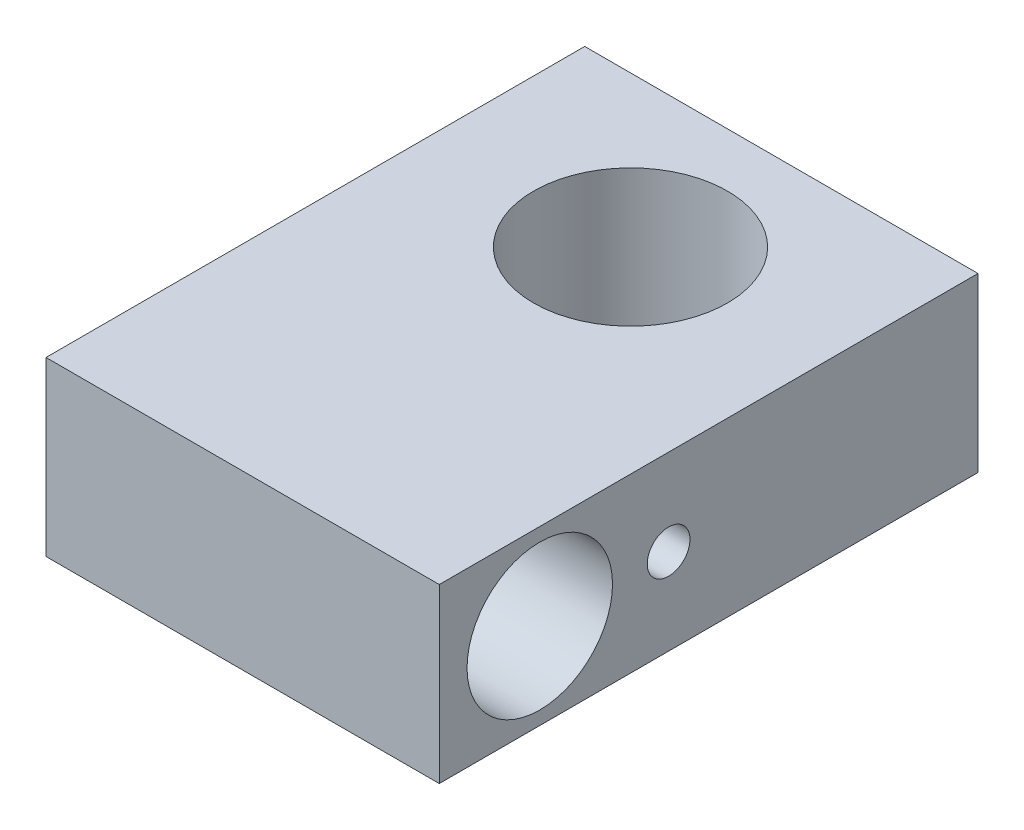
SolidWorks part; units mm, degrees
material "6061-T6 (SS)"
ref_plane "Front Plane" through (0, 0, 0) normal (0, 0, 1) x (1, 0, 0)
ref_plane "Top Plane" through (0, 0, 0) normal (0, 1, 0) x (1, 0, 0)
ref_plane "Right Plane" through (0, 0, 0) normal (1, 0, 0) x (0, 0, -1)
sketch "Sketch1" plane through (0, 0, 0) normal (0, 1, 0) x (1, 0, 0)
  line L0 (9.125, 7) -> (9.125, -18)
  line L1 (9.125, -18) -> (-9.125, -18)
  line L2 (-9.125, -18) -> (-9.125, 7)
  line L4 (-9.125, 7) -> (9.125, 7)
  line L8 (0, 0) -> (0, 7) construction
  point P4 (9.125, -18)
  point P6 (-9.125, -18)
  point P11 (-9.125, 7)
  point P12 (9.125, 7)
  dimension "D1" = 7
  dimension "D2" = 25
  dimension "D3" = 18.25
extrude "Boss-Extrude1" add sketch "Sketch1" along normal blind 8
hole_wizard "M10x1.0 Tapped Hole1" positions "Sketch3" profile "Sketch2" tap size "M10x1.0" standard "Ansi Metric" end condition through all
sketch "Sketch3" plane through (0, 8, 0) normal (0, 1, 0) x (-1, 0, 0)
  point P0 (0, 0)
sketch "Sketch2" plane through (0, 8, 0) normal (1, 0, 0) x (0, 0, 1)
  line L0 (0, 0) -> (0, 8)
  line L1 (0, 8) -> (4.5, 8)
  line L2 (4.5, 8) -> (4.5, 0)
  line L5 (4.5, 0) -> (0, 0)
  line L11 (0, -6.35) -> (0, 107.95) construction
  dimension "Thru Tap Drill Dia." = 9
  dimension "Thru Tap Drill Depth" = 8
cosmetic thread "Hole Thread1" parameters "D2"=10
sketch "Sketch7" plane through (9.125, 0, 0) normal (1, 0, 0) x (0, 0, -1)
  line L0 (-18, 4) -> (-13.3362, 4) construction
  line L1 (-18, 8) -> (-18, 0) construction
  circle A0 centre (-13.3362, 4) radius 3.375
  circle A1 centre (-7.3575, 4) radius 0.9906
  dimension "D1" = 6.75
  dimension "D3" = 1.9812
  dimension "D4" = 7.3575
  dimension "D5" = 13.3362
extrude "Cut-Extrude2" cut sketch "Sketch7" against normal through all
